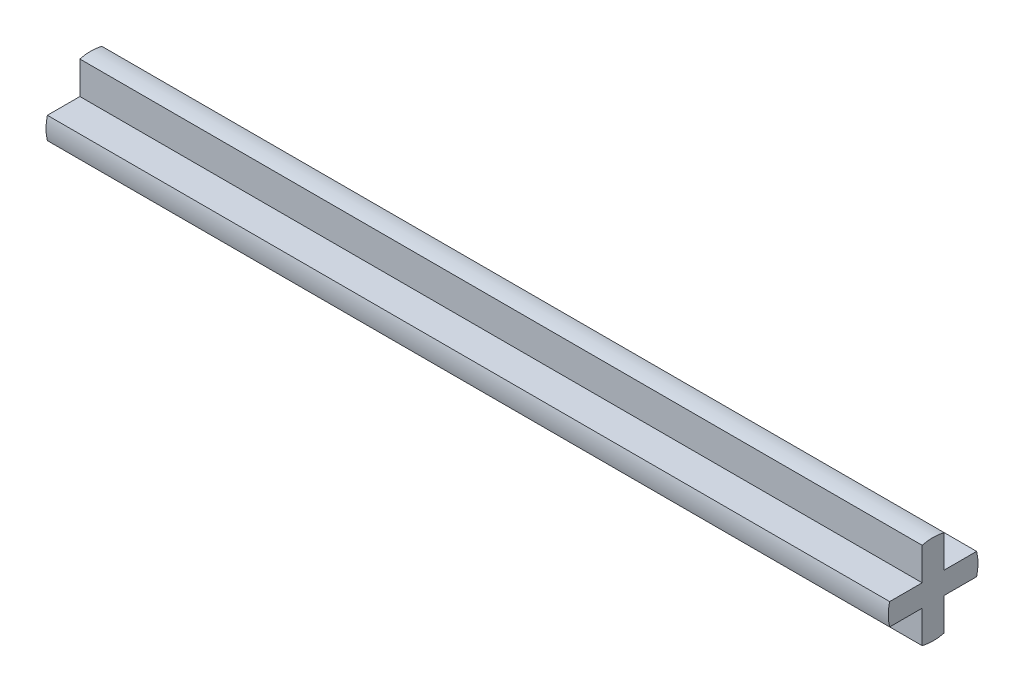
SolidWorks part; units mm, degrees
ref_plane "前视基准面" through (0, 0, 0) normal (0, 0, 1) x (1, 0, 0)
ref_plane "上视基准面" through (0, 0, 0) normal (0, 1, 0) x (1, 0, 0)
ref_plane "右视基准面" through (0, 0, 0) normal (1, 0, 0) x (0, 0, -1)
sketch "草图1" plane through (0, 0, 0) normal (1, 0, 0) x (0, 0, -1)
  circle A0 centre (0, 0) radius 2.45
extrude "凸台-拉伸1" add sketch "草图1" along normal mid plane 46
sketch "草图2" plane through (23, 0, 0) normal (1, 0, 0) x (0, 0, -1)
  line L0 (-3, 0.6) -> (-0.6, 0.6)
  line L1 (0.6, -3) -> (-0.6, -3)
  line L2 (3, -0.6) -> (3, 0.6)
  line L3 (0.6, 3) -> (-0.6, 3)
  line L4 (-3, -0.6) -> (-3, 0.6)
  line L5 (3, -3) -> (-3, 3) construction
  line L6 (3, 3) -> (-3, -3) construction
  line L7 (-0.6, 0.6) -> (-0.6, 3)
  line L8 (0.6, 0.6) -> (0.6, 3)
  line L9 (0.6, 0.6) -> (3, 0.6)
  line L10 (-0.6, -0.6) -> (-3, -0.6)
  line L11 (-0.6, -0.6) -> (-0.6, -3)
  line L12 (0.6, -0.6) -> (0.6, -3)
  line L13 (0.6, -0.6) -> (3, -0.6)
  point P0 (0, 0)
extrude "切除-拉伸1" cut sketch "草图2" against normal through all flip side to cut
